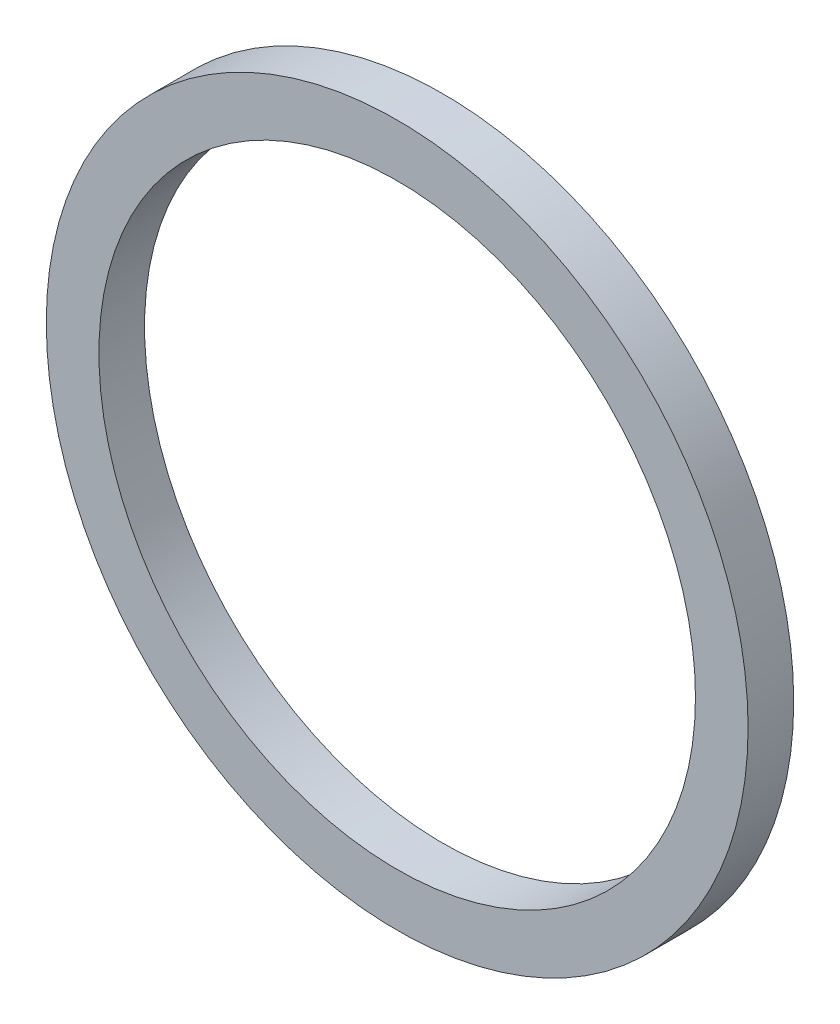
SolidWorks part; units mm, degrees
ref_plane "Front Plane" through (0, 0, 0) normal (0, 0, 1) x (1, 0, 0)
ref_plane "Top Plane" through (0, 0, 0) normal (0, 1, 0) x (1, 0, 0)
ref_plane "Right Plane" through (0, 0, 0) normal (1, 0, 0) x (0, 0, -1)
sketch "Sketch1" plane through (0, 0, 0) normal (0, 0, 1) x (1, 0, 0)
  circle A0 centre (0, 0) radius 10
  circle A1 centre (0, 0) radius 8.5
  dimension "D1" = 20
  dimension "D2" = 17
extrude "Boss-Extrude1" add sketch "Sketch1" along normal blind 1.3
